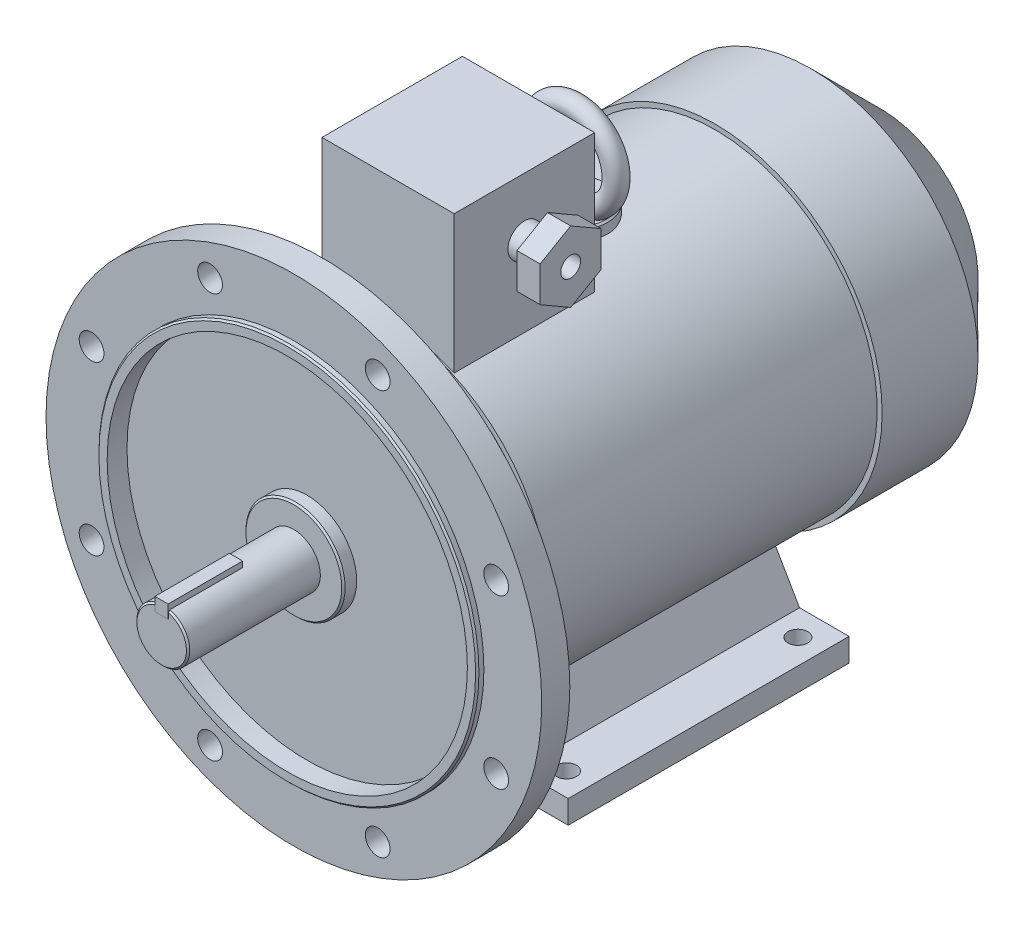
SolidWorks part; units mm, degrees
material "Ст.3 ГОСТ 380-88"
ref_plane "Спереди" through (0, 0, 0) normal (0, 0, 1) x (1, 0, 0)
ref_plane "Сверху" through (0, 0, 0) normal (0, 1, 0) x (1, 0, 0)
ref_plane "Справа" through (0, 0, 0) normal (1, 0, 0) x (0, 0, -1)
sketch "Эскиз1" plane through (0, 0, 0) normal (0, 0, 1) x (1, 0, 0)
  circle A0 centre (0, 0) radius 16
  dimension "D1" = 32
extrude "Вытянуть1" add sketch "Эскиз1" along normal blind 80
sketch "Эскиз2" plane through (0, 0, 0) normal (0, 0, -1) x (-1, 0, 0)
  circle A0 centre (0, 0) radius 150
  dimension "D1" = 300
extrude "Вытянуть2" add sketch "Эскиз2" along normal blind 17
sketch "Эскиз3" plane through (0, 0, 80) normal (0, 0, 1) x (1, 0, 0)
  line L0 (0, 0) -> (0, 28.3805) construction
  line L2 (-4, 19) -> (4, 19)
  line L3 (-4, 19) -> (-4, 11)
  line L4 (-4, 11) -> (4, 11)
  line L5 (4, 19) -> (4, 11)
  circle A2 centre (0, 0) radius 16 construction
  dimension "D1" = 8
  dimension "D2" = 8
  dimension "D3" = 35
extrude "Вытянуть3" add sketch "Эскиз3" against normal blind 45 and the other way blind 0.1
sketch "Эскиз4" plane through (0, 0, 0) normal (0, 0, 1) x (1, 0, 0)
  circle A0 centre (0, 0) radius 115
  circle A1 centre (0, 0) radius 109
  dimension "D1" = 230
  dimension "D2" = 218
extrude "Вытянуть4" add sketch "Эскиз4" along normal blind 4
sketch "Эскиз5" plane through (0, 0, 0) normal (0, 0, 1) x (1, 0, 0)
  circle A0 centre (0, 0) radius 109
  circle A1 centre (0, 0) radius 30
  dimension "D1" = 218
  dimension "D2" = 60
extrude "Вырез-Вытянуть1" cut sketch "Эскиз5" against normal blind 8
chamfer "Фаска1" distance 1 angle 45 3 edges at (115, 0, 4) (30, 0, 0) (0, -16, 80)
sketch "Эскиз6" plane through (0, 0, 0) normal (0, 0, 1) x (1, 0, 0)
  line L0 (0, 0) -> (0, 187.3141) construction
  line L1 (0, 0) -> (-70.131, 169.3113) construction
  circle A0 centre (-50.7056, 122.414) radius 7.5
  circle A3 centre (50.7056, 122.414) radius 7.5
  circle A4 centre (122.414, 50.7056) radius 7.5
  circle A5 centre (122.414, -50.7056) radius 7.5
  circle A6 centre (50.7056, -122.414) radius 7.5
  circle A7 centre (-50.7056, -122.414) radius 7.5
  circle A8 centre (-122.414, -50.7056) radius 7.5
  circle A9 centre (-122.414, 50.7056) radius 7.5
  dimension "D2" = 15
  dimension "D1" = 22.5
  dimension "D3" = 132.5
  dimension "D4" = 132.5
  dimension "D5" = 132.5
extrude "Вырез-Вытянуть2" cut sketch "Эскиз6" against normal through all
sketch "Эскиз7" plane through (0, 0, -17) normal (0, 0, -1) x (-1, 0, 0)
  circle A0 centre (0, 0) radius 95
  dimension "D1" = 190
extrude "Вытянуть5" add sketch "Эскиз7" along normal blind 39
sketch "Эскиз8" plane through (0, 0, -56) normal (0, 0, -1) x (-1, 0, 0)
  circle A0 centre (0, 0) radius 98
  dimension "D1" = 196
extrude "Вытянуть6" add sketch "Эскиз8" along normal blind 199
sketch "Эскиз9" plane through (0, 0, -255) normal (0, 0, -1) x (-1, 0, 0)
  circle A0 centre (0, 0) radius 101
  dimension "D1" = 202
extrude "Вытянуть7" add sketch "Эскиз9" along normal blind 100
chamfer "Фаска2" distance 42 angle 45 1 edges at (-101, 0, -355)
sketch "Эскиз10" plane through (0, 0, -56) normal (0, 0, 1) x (1, 0, 0)
  line L0 (0, 0) -> (0, -223.3518) construction
  line L1 (-110, -112) -> (-71.9171, -112)
  line L2 (-71.9171, -112) -> (-51.4404, -76.5333)
  line L3 (-51.4404, -76.5333) -> (-63.5648, -69.5333)
  line L4 (-63.5648, -69.5333) -> (-80, -98)
  line L5 (-80, -98) -> (-110, -98)
  line L6 (-110, -98) -> (-110, -112)
  line L7 (110, -98) -> (110, -112)
  line L8 (80, -98) -> (110, -98)
  line L9 (63.5648, -69.5333) -> (80, -98)
  line L10 (51.4404, -76.5333) -> (63.5648, -69.5333)
  line L11 (71.9171, -112) -> (51.4404, -76.5333)
  line L12 (110, -112) -> (71.9171, -112)
  dimension "D1" = 14
  dimension "D2" = 14
  dimension "D3" = 30
  dimension "D4" = 110
  dimension "D5" = 80
  dimension "D6" = 112
  dimension "D7" = 92
extrude "Вытянуть8" add sketch "Эскиз10" against normal blind 170
sketch "Эскиз11" plane through (0, -112, 0) normal (0, -1, 0) x (1, 0, 0)
  line L0 (-95, -70) -> (136.4638, -70) construction
  line L1 (15, 80) -> (-15, 80) construction
  line L2 (0, 0) -> (0, -248.1958) construction
  line L3 (95, -70) -> (-95, -70) construction
  line L4 (95, -70) -> (95, -210) construction
  circle A0 centre (95, -70) radius 6
  circle A1 centre (-95, -70) radius 6
  circle A2 centre (95, -210) radius 6
  circle A3 centre (-95, -210) radius 6
  dimension "D2" = 12
  dimension "D5" = 140
  dimension "D1" = 150
  dimension "D3" = 95
  dimension "D4" = 90
  dimension "D6" = 190
  dimension "D7" = 190
  dimension "D8" = 70
  dimension "D9" = 210
extrude "Вырез-Вытянуть3" cut sketch "Эскиз11" against normal up to next
sketch "Эскиз12" plane through (0, 0, 0) normal (0, 1, 0) x (1, 0, 0)
  line L0 (0, 0) -> (0, 375.5268) construction
  line L2 (-40, 57) -> (40, 57)
  line L3 (-40, 57) -> (-40, 142)
  line L4 (-40, 142) -> (40, 142)
  line L5 (40, 57) -> (40, 142)
  line L6 (-98, 56) -> (98, 56) construction
  dimension "D1" = 85
  dimension "D2" = 80
  dimension "D3" = 1
extrude "Вытянуть9" add sketch "Эскиз12" along normal blind 173
sketch "Эскиз13" plane through (0, 0, 0) normal (0, 1, 0) x (1, 0, 0)
  line L0 (0, 0) -> (0, 261.3171) construction
  circle A0 centre (0, 170) radius 20
  dimension "D1" = 40
  dimension "D2" = 170
extrude "Вытянуть10" add sketch "Эскиз13" along normal blind 103
chamfer "Фаска3" distance 1 angle 45 1 edges at (0, 103, -150)
ref_plane "Плоскость1" through (0, 0, -170) normal (0, 0, 1) x (1, 0, 0)
sketch "Эскиз14" plane through (0, 0, -170) normal (0, 0, 1) x (1, 0, 0)
  line L0 (19, 103) -> (-19, 103) construction
  line L1 (0, 0) -> (0, 193.8662) construction
  circle A0 centre (0, 128) radius 25
  dimension "D1" = 50
sketch "Эскиз15" plane through (0, 0, 0) normal (1, 0, 0) x (0, 0, -1)
  line L0 (170, 153) -> (170, 103) construction
  line L1 (189, 103) -> (151, 103) construction
  circle A0 centre (170, 153) radius 6
  dimension "D1" = 12
  dimension "D2" = 50
sweep "По траектории1" add profiles "Эскиз15" path "Эскиз14"
sketch "Эскиз16" plane through (40, 0, 0) normal (1, 0, 0) x (0, 0, -1)
  line L0 (57, 173) -> (142, 173) construction
  line L1 (57, 173) -> (57, 89.4651) construction
  circle A0 centre (99.5, 138) radius 10
  dimension "D1" = 20
  dimension "D2" = 35
  dimension "D3" = 42.5
extrude "Вытянуть11" add sketch "Эскиз16" along normal blind 14
sketch "Эскиз17" plane through (54, 0, 0) normal (1, 0, 0) x (0, 0, -1)
  line L1 (99.5, 159.362) -> (81, 148.681)
  line L2 (81, 148.681) -> (81, 127.319)
  line L3 (81, 127.319) -> (99.5, 116.638)
  line L4 (99.5, 116.638) -> (118, 127.319)
  line L5 (118, 127.319) -> (118, 148.681)
  line L6 (118, 148.681) -> (99.5, 159.362)
  line L7 (99.5, 138) -> (99.5, 180.1702) construction
  circle A0 centre (99.5, 138) radius 18.5 construction
  circle A1 centre (99.5, 138) radius 10 construction
  dimension "D1" = 37
extrude "Вытянуть12" add sketch "Эскиз17" along normal blind 14
sketch "Эскиз18" plane through (68, 0, 0) normal (1, 0, 0) x (0, 0, -1)
  circle A0 centre (99.5, 138) radius 6
  circle A1 centre (99.5, 138) radius 10 construction
  dimension "D1" = 12
extrude "Вырез-Вытянуть4" cut sketch "Эскиз18" against normal blind 14
